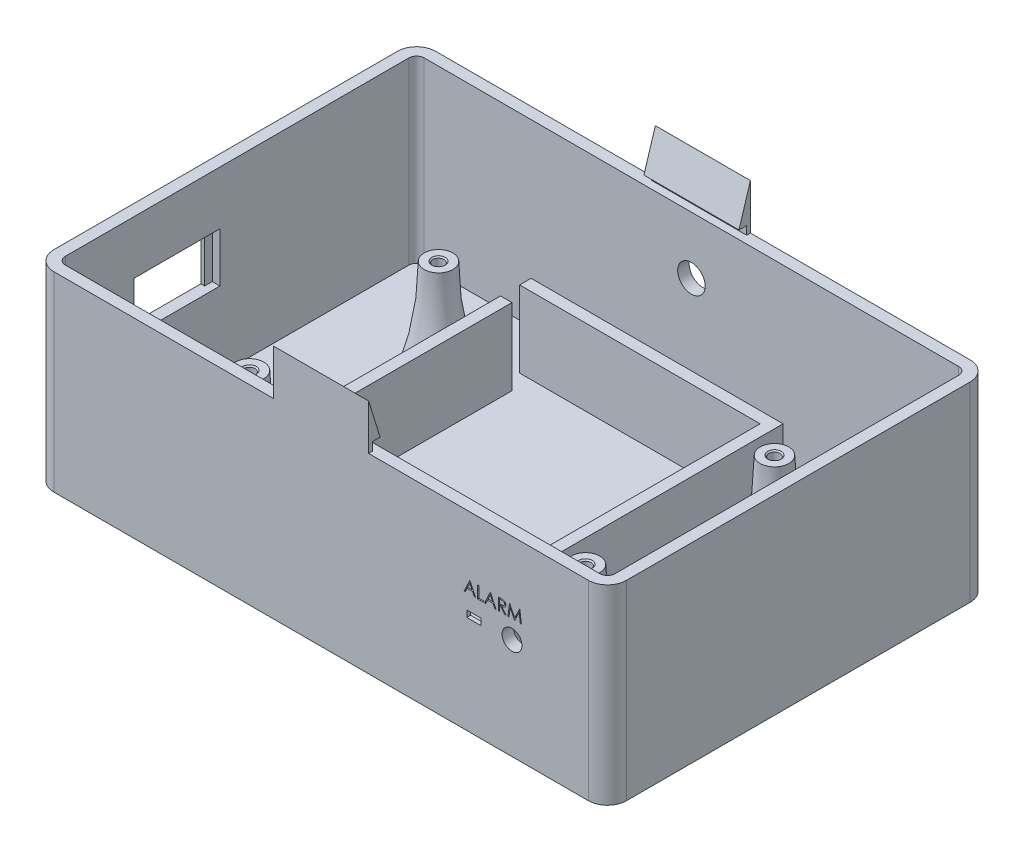
SolidWorks part; units mm, degrees
ref_plane "Front Plane" through (0, 0, 0) normal (0, 0, 1) x (1, 0, 0)
ref_plane "Top Plane" through (0, 0, 0) normal (0, 1, 0) x (1, 0, 0)
ref_plane "Right Plane" through (0, 0, 0) normal (1, 0, 0) x (0, 0, -1)
sketch "Sketch1" plane through (0, 0, 0) normal (0, 1, 0) x (1, 0, 0)
  line L1 (-75, -50) -> (75, -50)
  line L2 (-75, -50) -> (-75, 50)
  line L3 (-75, 50) -> (75, 50)
  line L4 (75, -50) -> (75, 50)
  line L5 (-75, -50) -> (75, 50) construction
  line L6 (-75, 50) -> (75, -50) construction
  point P0 (0, 0)
  dimension "D1" = 150
  dimension "D2" = 100
extrude "Boss-Extrude1" add sketch "Sketch1" along normal blind 50
fillet "Fillet1" radius 5 4 edges at (-75, 25, -50) (75, 25, -50) (75, 25, 50) (-75, 25, 50)
shell "Shell1" thickness 3
sketch "Sketch2" plane through (0, 3, 0) normal (0, 1, 0) x (1, 0, 0)
  line L0 (-33, -38) -> (-33, 38)
  line L1 (-30, -35) -> (30, -35)
  line L2 (-30, -35) -> (-30, 35)
  line L3 (-30, 35) -> (30, 35)
  line L4 (30, -35) -> (30, 35)
  line L5 (-30, -35) -> (30, 35) construction
  line L6 (-30, 35) -> (30, -35) construction
  line L7 (-33, 38) -> (33, 38)
  line L8 (33, -38) -> (33, 38)
  line L9 (-33, -38) -> (33, -38)
  point P0 (0, 0)
  dimension "D1" = 70
  dimension "D2" = 60
  dimension "D3" = 3
extrude "Boss-Extrude2" add sketch "Sketch2" along normal blind 20
sketch "Sketch3" plane through (-30, 0, 0) normal (1, 0, 0) x (0, 0, -1)
  line L0 (35, 3) -> (35, 23)
  line L1 (35, 23) -> (30, 23)
  line L2 (35, 23) -> (-35, 23) construction
  line L3 (30, 23) -> (30, 3)
  line L4 (35, 3) -> (-35, 3) construction
  line L5 (30, 3) -> (35, 3)
  dimension "D1" = 5
extrude "Cut-Extrude1" cut sketch "Sketch3" against normal up to surface (3 mm away) up to face at (-33, 13, 0)
sketch "Sketch4" plane through (0, 3, 0) normal (0, 1, 0) x (1, 0, 0)
  line L1 (-44, -24.75) -> (44, -24.75) construction
  line L2 (-44, -24.75) -> (-44, 24.75) construction
  line L3 (-44, 24.75) -> (44, 24.75) construction
  line L4 (44, -24.75) -> (44, 24.75) construction
  line L5 (-44, -24.75) -> (44, 24.75) construction
  line L6 (-44, 24.75) -> (44, -24.75) construction
  circle A0 centre (-44, 24.75) radius 2.75
  circle A1 centre (44, 24.75) radius 2.75
  circle A2 centre (-44, -24.75) radius 2.75
  circle A3 centre (44, -24.75) radius 2.75
  point P0 (0, 0)
  dimension "D3" = 5.5
  dimension "D1" = 88
  dimension "D2" = 49.5
extrude "Boss-Extrude3" add sketch "Sketch4" along normal blind 25 contours A0 | A2 | A1 | A3
hole_wizard "M3.5x0.6 Tapped Hole1" positions "Sketch6" profile "Sketch7" tap size "M3.5x0.6" standard "ANSI Metric"
sketch "Sketch6" plane through (0, 28, 0) normal (0, 1, 0) x (1, 0, 0)
  point P0 (-44, 24.75)
  point P3 (44, 24.75)
  point P6 (44, -24.75)
  point P9 (-44, -24.75)
sketch "Sketch7" plane through (-44, 28, -24.75) normal (1, 0, 0) x (0, 0, 1)
  line L0 (0, 0) -> (0, 25.8712)
  line L1 (0, 25.8712) -> (1.45, 25)
  line L2 (1.45, 25) -> (1.45, 0.325)
  line L3 (1.45, 0.325) -> (1.775, 0)
  line L5 (1.775, 0) -> (0, 0)
  line L6 (-1.45, 0.325) -> (-1.775, 0) construction
  line L10 (0, 25.8712) -> (-1.45, 25) construction
  line L11 (0, -6.35) -> (0, 107.95) construction
  dimension "Tap Drill Dia." = 2.9
  dimension "Tap Drill Depth" = 25
  dimension "Near C'Sink Dia." = 3.55
  dimension "Near C'Sink Angle" = 90
  dimension "Drill Angle" = 118
cosmetic thread "Hole Thread1" parameters "D1"=7, "D2"=3.5
cosmetic thread "Hole Thread2" parameters "D1"=7, "D2"=3.5
cosmetic thread "Hole Thread3" parameters "D1"=7, "D2"=3.5
cosmetic thread "Hole Thread4" parameters "D1"=7, "D2"=3.5
ref_plane "Plane1" through (0, 0, -24.75) normal (0, 0, 1) x (1, 0, 0)
sketch "Sketch8" plane through (0, 0, -24.75) normal (0, 0, 1) x (1, 0, 0)
  line L0 (-41.25, 3) -> (-41.25, 28)
  line L1 (-41.25, 28) -> (-40.25, 28)
  line L2 (-41.25, 3) -> (-36.25, 3)
  line L3 (-41.25, 3) -> (-46.75, 3) construction
  line L4 (-44, 3) -> (-44, 43.6967) construction
  arc A0 (-40.25, 28) -> (-36.25, 3) centre (39.875, 28) ccw
  dimension "D1" = 5
  dimension "D2" = 1
revolve "Revolve1" add sketch "Sketch8" angle 360 about L4
pattern_linear "LPattern1" count 2 spacing 88 along (1, 0, 0) count 2 spacing 49.5 along (0, 0, 1) of "Revolve1"
sketch "Sketch9" plane through (0, 3, 0) normal (0, 1, 0) x (1, 0, 0)
  line L0 (72, -45) -> (72, 45) construction
  line L1 (66, -12) -> (68, -12)
  line L2 (66, -12) -> (66, 12)
  line L3 (66, 12) -> (68, 12)
  line L4 (68, -12) -> (68, 12)
  line L5 (66, -12) -> (68, 12) construction
  line L6 (66, 12) -> (68, -12) construction
  point P0 (67, 0)
  dimension "D1" = 2
  dimension "D2" = 24
  dimension "D3" = 5
extrude "Cut-Extrude2" cut sketch "Sketch9" against normal through all
sketch "Sketch10" plane through (-72, 0, 0) normal (1, 0, 0) x (0, 0, -1)
  line L1 (-25, 23) -> (-6.5, 23)
  line L2 (-25, 23) -> (-25, 36)
  line L3 (-25, 36) -> (-6.5, 36)
  line L4 (-6.5, 23) -> (-6.5, 36)
  line L5 (-25, 23) -> (-6.5, 36) construction
  line L6 (-25, 36) -> (-6.5, 23) construction
  line L7 (45, 3) -> (-45, 3) construction
  line L8 (-45, 3) -> (-45, 50) construction
  point P0 (-15.75, 29.5)
  dimension "D1" = 18.5
  dimension "D2" = 13
  dimension "D3" = 20
  dimension "D4" = 20
extrude "Cut-Extrude3" cut sketch "Sketch10" against normal through all
sketch "Sketch11" plane through (-72, 0, 0) normal (1, 0, 0) x (0, 0, -1)
  line L0 (-15.75, 23) -> (-15.75, 36) construction
  line L1 (-6.5, 36) -> (-4.5, 36)
  line L2 (-6.5, 36) -> (-6.5, 23)
  line L3 (-6.5, 23) -> (-4.5, 23)
  line L4 (-4.5, 36) -> (-4.5, 23)
  line L5 (-25, 23) -> (-6.5, 23) construction
  line L6 (-6.5, 36) -> (-25, 36) construction
  line L7 (-25, 23) -> (-27, 23)
  line L8 (-25, 36) -> (-25, 23)
  line L9 (-25, 36) -> (-27, 36)
  line L10 (-27, 36) -> (-27, 23)
  dimension "D1" = 13
  dimension "D2" = 2
extrude "Cut-Extrude4" cut sketch "Sketch11" against normal blind 2
sketch "Sketch12" plane through (0, 0, -47) normal (0, 0, 1) x (1, 0, 0)
  line L0 (70, 50) -> (-70, 50) construction
  circle A0 centre (0, 35) radius 3.6
  dimension "D1" = 7.2
  dimension "D2" = 15
extrude "Cut-Extrude5" cut sketch "Sketch12" against normal through all
sketch "Sketch13" plane through (0, 0, 47) normal (0, 0, -1) x (-1, 0, 0)
  line L0 (-70, 3) -> (-70, 50) construction
  line L2 (-41.85, 25.65) -> (-38.15, 25.65)
  line L3 (-41.85, 25.65) -> (-41.85, 27.35)
  line L4 (-41.85, 27.35) -> (-38.15, 27.35)
  line L5 (-38.15, 25.65) -> (-38.15, 27.35)
  line L6 (-41.85, 25.65) -> (-38.15, 27.35) construction
  line L7 (-41.85, 27.35) -> (-38.15, 25.65) construction
  circle A0 centre (-50, 26.5) radius 2.6
  point P4 (-70, 26.5)
  point P5 (-40, 26.5)
  dimension "D1" = 5.2
  dimension "D2" = 20
  dimension "D3" = 10
  dimension "D4" = 3.7
  dimension "D5" = 1.7
extrude "Cut-Extrude6" cut sketch "Sketch13" against normal through all
sketch "Sketch14" plane through (0, 0, 47) normal (0, 0, -1) x (-1, 0, 0)
  line L1 (-45.1, 24.4) -> (-34.9, 24.4)
  line L2 (-45.1, 24.4) -> (-45.1, 28.6)
  line L3 (-45.1, 28.6) -> (-34.9, 28.6)
  line L4 (-34.9, 24.4) -> (-34.9, 28.6)
  line L5 (-45.1, 24.4) -> (-34.9, 28.6) construction
  line L6 (-45.1, 28.6) -> (-34.9, 24.4) construction
  line L7 (70, 50) -> (-70, 50) construction
  circle A0 centre (-50, 26.5) radius 2.6 construction
  point P0 (-40, 26.5)
  dimension "D1" = 10
  dimension "D2" = 23.5
  dimension "D3" = 4.2
  dimension "D4" = 10.2
extrude "Cut-Extrude7" cut sketch "Sketch14" against normal blind 2
sketch "Sketch15" plane through (0, 0, 50) normal (0, 0, 1) x (1, 0, 0)
  text T0 "ALARM"
extrude "Cut-Extrude8" cut sketch "Sketch15" against normal blind 1
sketch "Sketch16" plane through (0, 0, 50) normal (0, 0, 1) x (1, 0, 0)
  line L0 (-70, 50) -> (70, 50) construction
  line L1 (12.45, 50) -> (-12.45, 50)
  line L2 (12.45, 50) -> (12.45, 61.9)
  line L3 (12.45, 61.9) -> (-12.45, 61.9)
  line L4 (-12.45, 50) -> (-12.45, 61.9)
  line L5 (-70, 50) -> (70, 50) construction
  point P6 (0, 50)
  point P7 (0, 50)
  dimension "D1" = 24.9
  dimension "D2" = 11.9
extrude "Boss-Extrude4" add sketch "Sketch16" against normal blind 3
sketch "Sketch17" plane through (0, 0, 0) normal (0, 1, 0) x (1, 0, 0)
  line L0 (0, 0) -> (97.3733, 0) construction
sketch "Sketch18" plane through (12.45, 0, 0) normal (1, 0, 0) x (0, 0, -1)
  line L0 (-50, 61.9) -> (-47, 52.2)
  line L2 (-47, 52.2) -> (-47, 61.9)
  line L3 (-47, 61.9) -> (-50, 61.9)
  line L5 (-49, 52.2) -> (-49, 50)
  line L6 (-47, 50) -> (-50, 50) construction
  line L7 (-49, 50) -> (-47, 50)
  line L8 (-47, 50) -> (-47, 52.2)
  line L9 (-49, 52.2) -> (-47, 52.2)
  dimension "D1" = 2.2
  dimension "D2" = 2
  dimension "D3" = 2.2
extrude "Cut-Extrude10" cut sketch "Sketch18" against normal through all
sketch "Sketch19" plane through (0, 0, -50) normal (0, 0, -1) x (-1, 0, 0)
  line L0 (-70, 50) -> (70, 50) construction
  line L1 (-12.45, 50) -> (12.45, 50)
  line L2 (-12.45, 50) -> (-12.45, 61.9)
  line L3 (-12.45, 61.9) -> (12.45, 61.9)
  line L4 (12.45, 50) -> (12.45, 61.9)
  line L5 (-70, 50) -> (70, 50) construction
  point P6 (0, 50)
  point P7 (0, 50)
  dimension "D1" = 24.9
  dimension "D2" = 11.9
extrude "Boss-Extrude5" add sketch "Sketch19" against normal blind 3
sketch "Sketch20" plane through (-12.45, 0, 0) normal (-1, 0, 0) x (0, 0, 1)
  line L0 (-50, 61.9) -> (-47, 52.2)
  line L1 (-47, 50) -> (-47, 61.9) construction
  line L2 (-47, 52.2) -> (-47, 61.9)
  line L3 (-47, 61.9) -> (-50, 61.9)
  line L4 (-47, 52.2) -> (-47, 50)
  line L5 (-47, 50) -> (-49, 50)
  line L6 (-45, 50) -> (-50, 50) construction
  line L7 (-49, 50) -> (-49, 52.2)
  line L8 (-47, 52.2) -> (-49, 52.2)
  line M5 (-50, 50) -> (-47, 50)
  line M6 (-47, 50) -> (-47, 61.9)
  line M7 (-47, 61.9) -> (-50, 61.9)
  dimension "D1" = 2.2
  dimension "D2" = 2
extrude "Cut-Extrude11" cut sketch "Sketch20" against normal through all contours L0 M7 M6 | L8 L7 M6 M5
